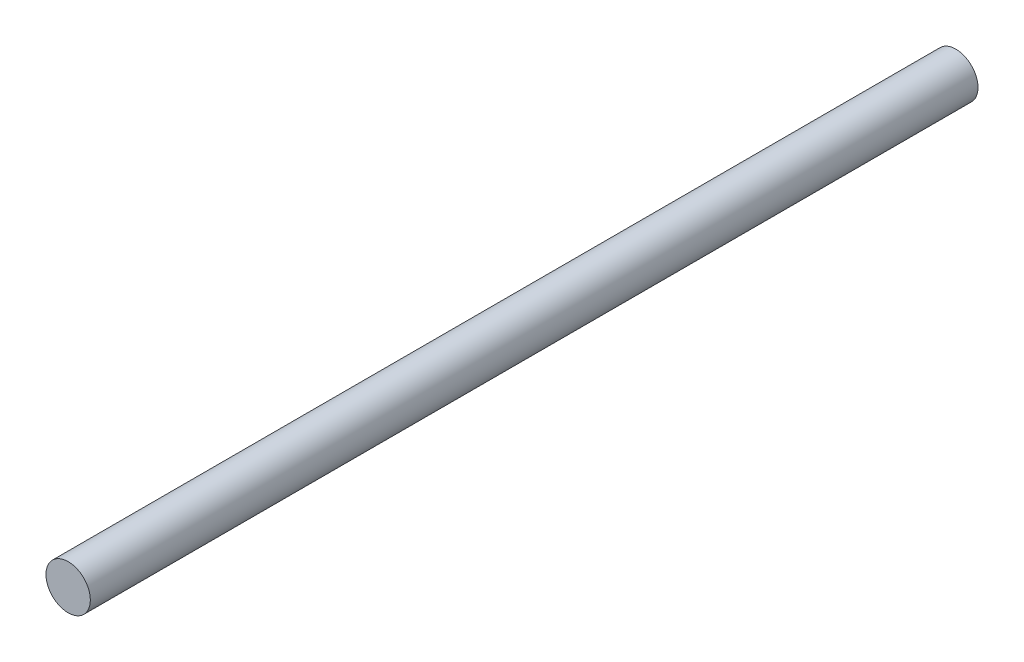
SolidWorks part; units mm, degrees
ref_plane "Front Plane" through (0, 0, 0) normal (0, 0, 1) x (1, 0, 0)
ref_plane "Top Plane" through (0, 0, 0) normal (0, 1, 0) x (1, 0, 0)
ref_plane "Right Plane" through (0, 0, 0) normal (1, 0, 0) x (0, 0, -1)
sketch "Sketch1" plane through (0, 0, 0) normal (0, 0, 1) x (1, 0, 0)
  circle A0 centre (0, 0) radius 3.175
  dimension "D1" = 6.35
extrude "Boss-Extrude1" add sketch "Sketch1" along normal blind 127
